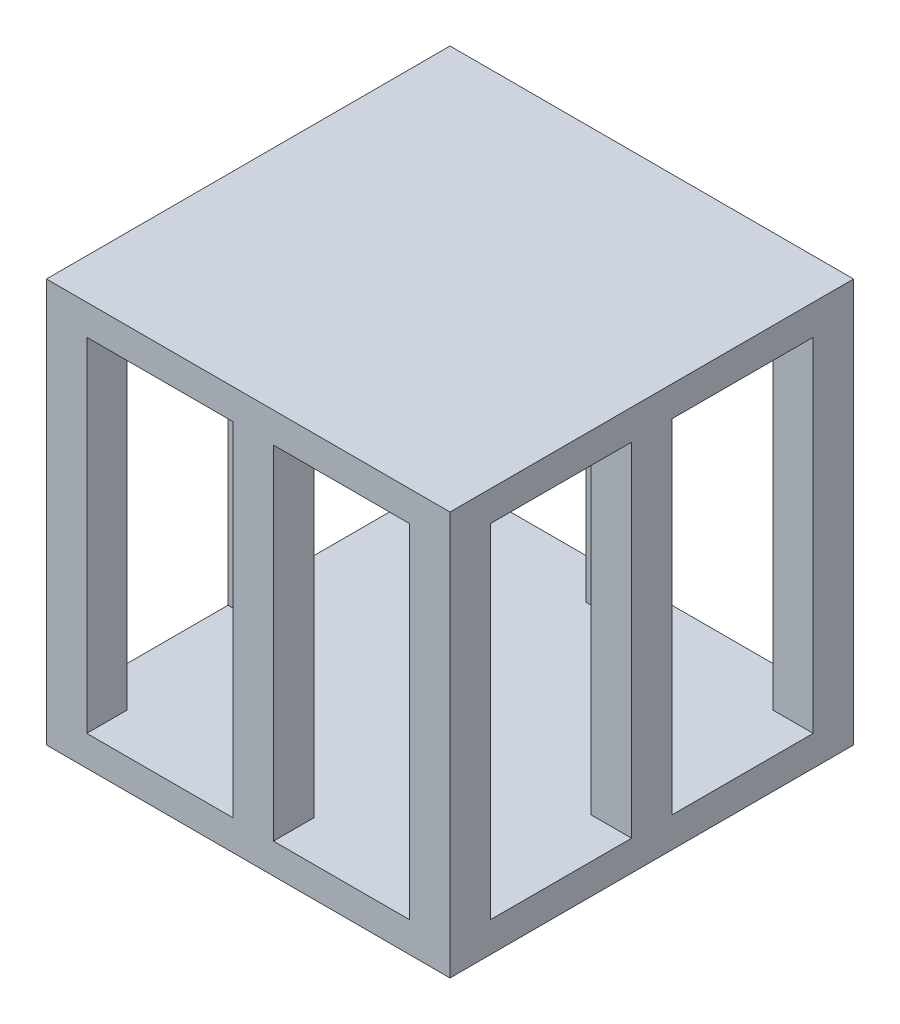
SolidWorks part; units mm, degrees
ref_plane "Front Plane" through (0, 0, 0) normal (0, 0, 1) x (1, 0, 0)
ref_plane "Top Plane" through (0, 0, 0) normal (0, 1, 0) x (1, 0, 0)
ref_plane "Right Plane" through (0, 0, 0) normal (1, 0, 0) x (0, 0, -1)
sketch "Sketch1" plane through (0, 0, 0) normal (0, 1, 0) x (1, 0, 0)
  line L1 (-25.4, -25.4) -> (25.4, -25.4)
  line L2 (-25.4, -25.4) -> (-25.4, 25.4)
  line L3 (-25.4, 25.4) -> (25.4, 25.4)
  line L4 (25.4, -25.4) -> (25.4, 25.4)
  line L5 (-25.4, -25.4) -> (25.4, 25.4) construction
  line L6 (-25.4, 25.4) -> (25.4, -25.4) construction
  line L7 (-25.4, -25.4) -> (-20.32, -25.4)
  line L8 (-25.4, -25.4) -> (-25.4, -20.32)
  line L9 (-25.4, -20.32) -> (-20.32, -20.32)
  line L10 (-20.32, -25.4) -> (-20.32, -20.32)
  point P0 (0, 0)
extrude "Boss-Extrude1" add sketch "Sketch1" along normal mid plane 43.18 contours L1 L10 L9 L2
pattern_linear "LPattern2" count 3 spacing 22.86 along (0, 0, -1) of "Boss-Extrude1"
mirror "Mirror1" about plane through (0, 0, 0) normal (1, 0, 0) of bodies 104 103 101
pattern_linear "LPattern3" count 2 spacing 23.495 along (1, 0, 0) of bodies 101
pattern_linear "LPattern4" count 2 spacing 23.495 along (-1, 0, 0) of bodies 106
sketch "Sketch2" plane through (0, 21.59, 0) normal (0, 1, 0) x (1, 0, 0)
  line L1 (25.4, -25.4) -> (-25.4, -25.4)
  line L2 (25.4, -25.4) -> (25.4, 25.4)
  line L3 (25.4, 25.4) -> (-25.4, 25.4)
  line L4 (-25.4, -25.4) -> (-25.4, 25.4)
extrude "Boss-Extrude3" add sketch "Sketch2" along normal blind 3.81
sketch "Sketch3" plane through (0, -21.59, 0) normal (0, -1, 0) x (1, 0, 0)
  line L1 (25.4, 25.4) -> (-25.4, 25.4)
  line L2 (25.4, 25.4) -> (25.4, -25.4)
  line L3 (25.4, -25.4) -> (-25.4, -25.4)
  line L4 (-25.4, 25.4) -> (-25.4, -25.4)
extrude "Boss-Extrude4" add sketch "Sketch3" along normal blind 3.81
